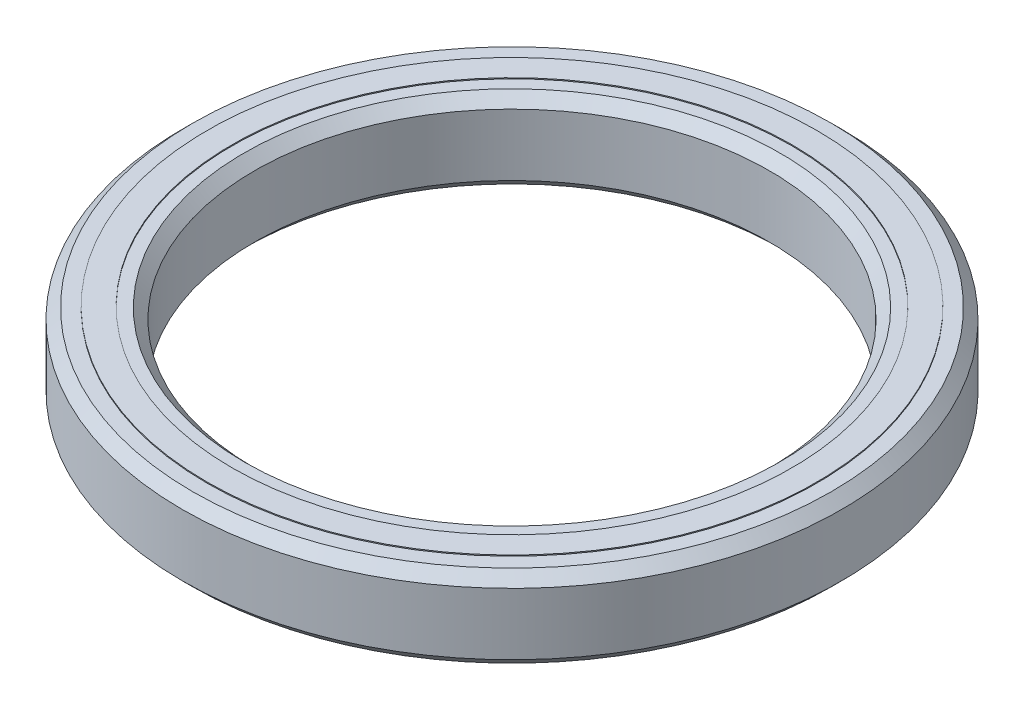
SolidWorks part; units mm, degrees
material "Acero aleado"
ref_plane "Alzado" through (0, 0, 0) normal (0, 0, 1) x (1, 0, 0)
ref_plane "Planta" through (0, 0, 0) normal (0, 1, 0) x (1, 0, 0)
ref_plane "Vista lateral" through (0, 0, 0) normal (1, 0, 0) x (0, 0, -1)
sketch "Croquis1" plane through (0, 0, 0) normal (0, 1, 0) x (1, 0, 0)
  circle A0 centre (0, 0) radius 16
  circle A1 centre (0, 0) radius 12.5
  dimension "D1" = 25
  dimension "D2" = 32
extrude "Saliente-Extruir1" add sketch "Croquis1" along normal mid plane 4
chamfer "Chaflán1" distance 0.5 angle 45 4 edges at (0, -2, 12.5) (0, 2, 12.5) (0, -2, 16) (0, 2, 16)
sketch "Croquis2" plane through (0, 0, 0) normal (0, 1, 0) x (1, 0, 0)
  circle A0 centre (0, 0) radius 13.5905
  circle A1 centre (0, 0) radius 14.7935
extrude "Saliente-Extruir2" add sketch "Croquis2" along normal mid plane 4.1
